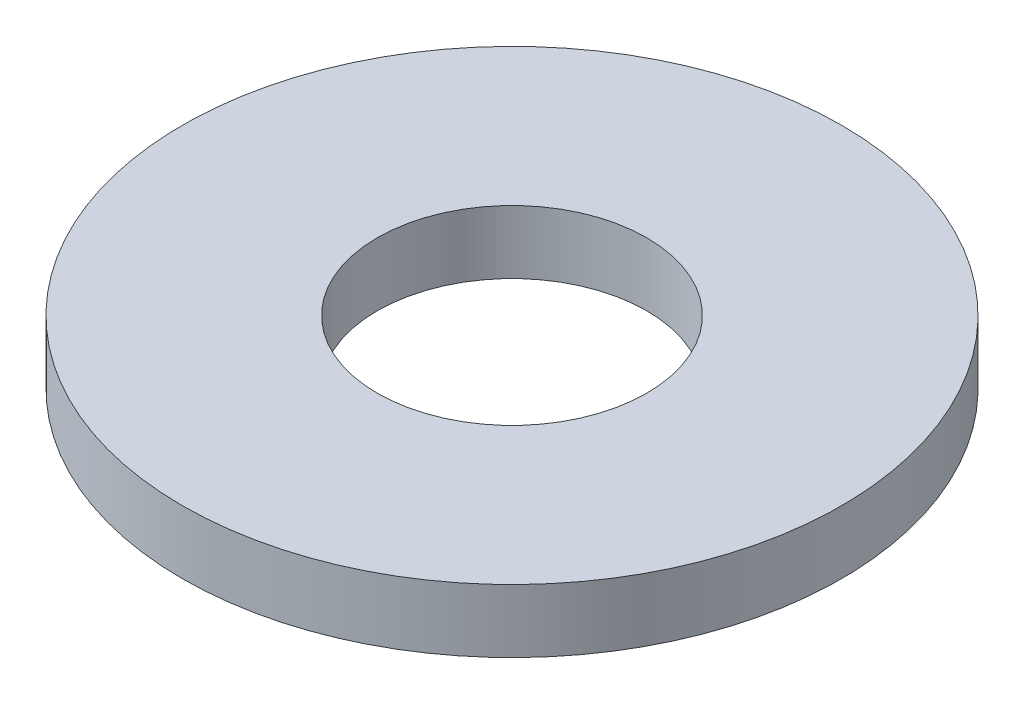
SolidWorks part; units mm, degrees
ref_plane "Front Plane" through (0, 0, 0) normal (0, 0, 1) x (1, 0, 0)
ref_plane "Top Plane" through (0, 0, 0) normal (0, 1, 0) x (1, 0, 0)
ref_plane "Right Plane" through (0, 0, 0) normal (1, 0, 0) x (0, 0, -1)
sketch "Sketch1" plane through (0, 0, 0) normal (0, 1, 0) x (1, 0, 0)
  circle A0 centre (0, 0) radius 17.4625
  dimension "OD" = 34.925
extrude "Boss-Extrude1" add sketch "Sketch1" along normal blind 3.3528
sketch "Sketch5" plane through (0, 3.3528, 0) normal (0, 1, 0) x (-1, 0, 0)
  circle A0 centre (0, 0) radius 7.1374
  dimension "ID" = 14.2748
extrude "Cut-Extrude1" cut sketch "Sketch5" against normal through all
